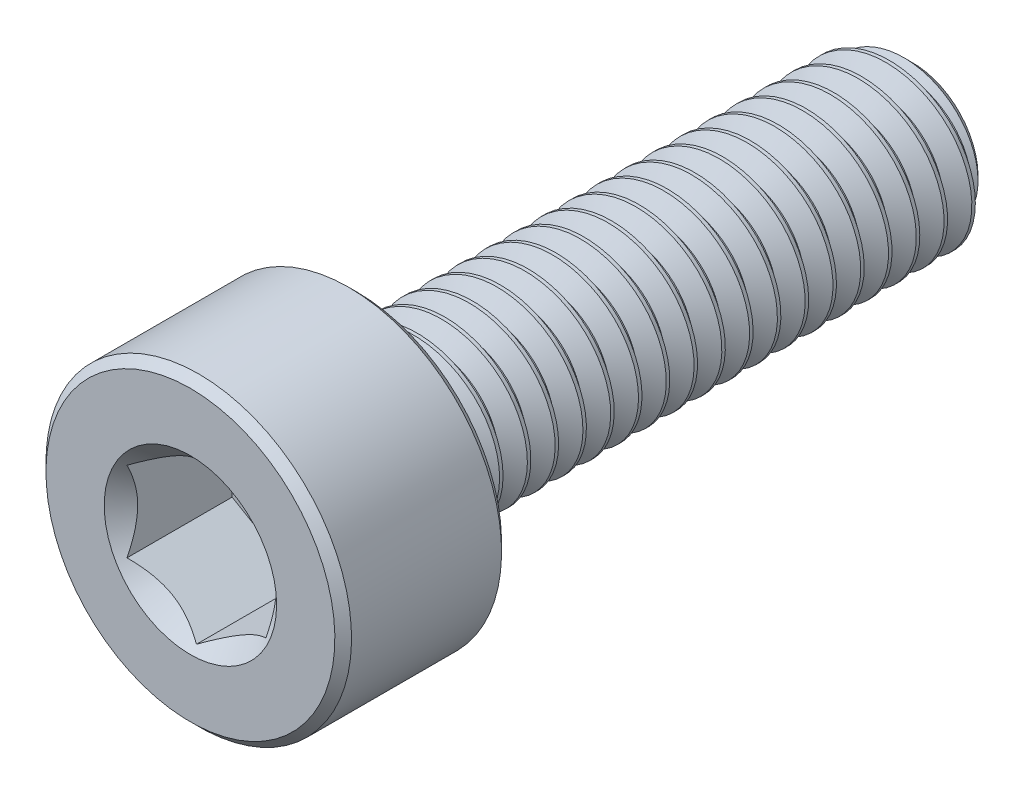
SolidWorks part; units mm, degrees
ref_plane "Front Plane" through (0, 0, 0) normal (0, 0, 1) x (1, 0, 0)
ref_plane "Top Plane" through (0, 0, 0) normal (0, 1, 0) x (1, 0, 0)
ref_plane "Right Plane" through (0, 0, 0) normal (1, 0, 0) x (0, 0, -1)
sketch "Sketch1" plane through (0, 0, 0) normal (1, 0, 0) x (0, 0, -1)
  line L0 (-6.5, 0) -> (6.5, 0) construction
  line L1 (6.5, 0) -> (6.5, 1.1752) construction
  line L2 (6.5, 1.1752) -> (6.1752, 1.5) construction
  line L3 (6.1752, 1.5) -> (6.125, 1.5) construction
  line L4 (6.125, 1.5) -> (-3.5, 1.5) construction
  line L5 (-3.5, 1.5) -> (-3.5, 2.75) construction
  line L6 (-3.5, 2.75) -> (-6.5, 2.75) construction
  line L7 (-6.5, 2.75) -> (-6.5, 0) construction
  line L8 (6.5, 1.1752) -> (6.5, 1.5) construction
  line L9 (6.4688, 1.5541) -> (6.7188, 1.1211) construction
  line L10 (6.7188, 1.1211) -> (6.9687, 1.5541) construction
  line L11 (6.9687, 1.5541) -> (6.4688, 1.5541) construction
  line L12 (6.7188, 1.5541) -> (6.7188, 1.5) construction
  line L13 (6.7188, 1.1211) -> (6.7188, 1.1752) construction
  line L14 (6.6875, 1.1752) -> (6.75, 1.1752) construction
  line L15 (6.5, 1.5) -> (6.9375, 1.5) construction
  line L16 (6.4844, 1.5271) -> (6.9531, 1.5271) construction
  line L17 (6.5, 0) -> (6.5, -1.5) construction
  line L18 (-3.65, 2.75) -> (-3.5, 2.6) construction
  line L19 (-6.35, 2.75) -> (-6.5, 2.6) construction
  line L20 (-3.5, 1.5) -> (-3.5, 0) construction
  line L21 (-3.5, 0.75) -> (-0.1667, 0.75) construction
  line L22 (-0.1667, 0.75) -> (3.1667, 0.75) construction
  line L23 (3.1667, 0.75) -> (6.5, 0.75) construction
  line L24 (-0.1667, 0.75) -> (-0.1667, 1.5) construction
  line L25 (-0.1667, 1.5) -> (-0.1667, 2.75) construction
  line L26 (3.1667, 0.75) -> (3.1667, 2.75) construction
  point P0 (-6.5, 1.25)
  point P3 (5.25, 1.5)
  point P4 (0, 0)
  point P18 (3.1667, 1.5)
  point P22 (6.7188, 1.1752)
  point P24 (6.125, 1.5)
  point P25 (6.7188, 1.5)
  point P28 (6.7187, 1.5271)
  point P29 (5.25, -1.5)
  point P30 (-0.1667, 1.5)
  point P31 (-5, 2.75)
  point P37 (-4.025, 2.75)
  point P38 (-6.275, 2.75)
  point P45 (-0.1667, 0.75)
  point P46 (3.1667, 0.75)
  dimension "D2" = 0.0625
  dimension "D7" = 0.15
  dimension "D8" = 0.15
  dimension "D9" = 0.15
  dimension "D10" = 0.075
  dimension "D11" = 0.375
  dimension "Drive Size" = 2.5
  dimension "Head Diameter" = 5.5
  dimension "Head Height" = 3
  dimension "Thread Pitch" = 0.5
  dimension "Thread Dia" = 3
  dimension "Length" = 10
  dimension "D12" = 0.375
  dimension "D4" = 1.25
  dimension "D3" = 45
sketch "Sketch2" plane through (0, 0, 0) normal (1, 0, 0) x (0, 0, -1)
  line L0 (-6.5, 0) -> (-6.5, 2.6)
  line L1 (-6.35, 2.75) -> (-3.65, 2.75)
  line L2 (-3.5, 2.6) -> (-3.5, 1.65)
  line L4 (6.1752, 1.5) -> (6.5, 1.1752)
  line L5 (6.5, 1.1752) -> (6.5, 0)
  line L6 (-3.5, 2.75) -> (-6.5, 2.75) construction
  line L7 (6.5, 0) -> (-6.5, 0)
  line L8 (-6.35, 2.75) -> (-6.5, 2.6) construction
  line L10 (-6.35, 2.75) -> (-6.5, 2.6)
  line L14 (-3.65, 2.75) -> (-3.5, 2.6) construction
  line L16 (-3.65, 2.75) -> (-3.5, 2.6)
  line L17 (-3.5, 1.5) -> (-3.5, 2.75) construction
  line L19 (-3.35, 1.5) -> (6.1752, 1.5)
  line L20 (6.125, 1.5) -> (-3.5, 1.5) construction
  arc A1 (-3.5, 1.65) -> (-3.35, 1.5) centre (-3.35, 1.65) ccw
  dimension "D3" = 0.15
revolve "Revolve1" add sketch "Sketch2" angle 360 about L7
sketch "Sketch3" plane through (0, 0, 6.5) normal (0, 0, 1) x (1, 0, 0)
  line L1 (1.25, -0.7217) -> (1.25, 0.7217)
  line L2 (1.25, 0.7217) -> (0, 1.4434)
  line L3 (0, 1.4434) -> (-1.25, 0.7217)
  line L4 (-1.25, 0.7217) -> (-1.25, -0.7217)
  line L5 (-1.25, -0.7217) -> (0, -1.4434)
  line L6 (0, -1.4434) -> (1.25, -0.7217)
  circle A0 centre (0, 0) radius 1.25 construction
  circle A1 centre (0, 0) radius 2.75 construction
  circle A2 centre (0, 0) radius 2.75 construction
  circle A3 centre (0, 0) radius 1.4434 construction
  point P13 (0, 0)
  dimension "D1" = 2.8868
extrude "Cut-Extrude1" cut sketch "Sketch3" against normal offset from surface (2 mm away) 1 up to face at (0, 2.6, 3.5)
sketch "Sketch4" plane through (0, 0, 6.5) normal (0, 0, 1) x (1, 0, 0)
  circle A0 centre (0, 0) radius 1.5516
  dimension "D1" = 3.1033
extrude "Cut-Extrude2" cut sketch "Sketch4" against normal up to vertex (1.5 mm away) draft 45 up to point (0, 2.75, 5)
sketch "Sketch11" plane through (0, 0, 0) normal (1, 0, 0) x (0, 0, -1)
  line L0 (-6.5, 0) -> (6.5, 0) construction
  line L1 (-6.5, 0) -> (6.5, 0) construction
  line L2 (-1.625, 0) -> (-1.625, 1.5) construction
  line L3 (6.125, 1.5) -> (-3.5, 1.5) construction
  line L4 (4.625, 0) -> (4.625, 1.5) construction
  line L6 (6.5, 1.1752) -> (6.5, 1.5) construction
  point P2 (-1.625, 0)
  point P3 (4.625, 0)
  dimension "D1" = 1.875
  dimension "D2" = 1.875
sketch "Sketch6" plane through (0, 0, -6.5) normal (0, 0, -1) x (-1, 0, 0)
  circle A0 centre (0, 0) radius 1.5
curve "Helix/Spiral1" pitch 0.5 height 10.5 turns 21
sketch "Sketch10" plane through (0, 0, 0) normal (1, 0, 0) x (0, 0, -1)
  line L0 (-3.35, -2.75) -> (-3.35, 2.75)
  line L5 (-6.5, 0) -> (6.5, 0) construction
  line L6 (-3.35, 1.5) -> (-3.35, -1.5) construction
  point P3 (-3.35, 0)
split "Split1" trim tools "Sketch10" bodies to split 106 resulting bodies 114 115
sketch "Sketch7" plane through (0, 0, 0) normal (1, 0, 0) x (0, 0, -1)
  line L0 (6.4844, 1.5271) -> (6.9531, 1.5271)
  line L1 (6.9531, 1.5271) -> (6.75, 1.1752)
  line L2 (6.75, 1.1752) -> (6.6875, 1.1752)
  line L3 (6.6875, 1.1752) -> (6.4844, 1.5271)
sweep "Cut-Sweep1" cut profiles "Sketch7" path "Helix/Spiral1"
sketch "Sketch8" plane through (0, 0, 0) normal (1, 0, 0) x (0, 0, -1)
  line L0 (-3.5, 0) -> (-3.5, 1.5)
  line L1 (-3.35, -1.5) -> (-3.35, 1.5) construction
  line L2 (-3.5, 1.5) -> (-3.35, 1.5)
  line L4 (-3.35, 1.5) -> (-2.484, 0)
  line L5 (-2.484, 0) -> (-3.5, 0)
  line L6 (6.125, 1.5) -> (-3.5, 1.5) construction
  line L7 (-6.5, 0) -> (6.5, 0) construction
  dimension "D1" = 60
revolve "Revolve2" add sketch "Sketch8" angle 360 about L5
equation "\"D2@Sketch1\" = \"Thread Pitch@Sketch1\" / 8"
equation "\"D4@Helix/Spiral1\" = \"Thread Pitch@Sketch1\""
equation "\"D7@Sketch1\" = \"Head Height@Sketch1\" * .05"
equation "\"D8@Sketch1\"=\"D7@Sketch1\""
equation "\"D9@Sketch1\"=\"D7@Sketch1\""
equation "\"D10@Sketch1\"=\"D7@Sketch1\"/2"
equation "\"D11@Sketch1\"=\"D10@Sketch1\"*5"
equation "\"D4@Sketch1\"=\"Thread Pitch@Sketch1\"*2.5"
equation "\"D12@Sketch1\"=\"Thread Pitch@Sketch1\"*.75"
equation "\"D3@Helix/Spiral1\"=\"Length@Sketch1\"+\"Thread Pitch@Sketch1\""
equation "\"D3@Sketch2\"=\"Thread Dia@Sketch1\"*0.05"
equation "\"D1@Sketch11\"=\"Length@Sketch1\"*0.1875"
equation "\"D2@Sketch11\"=\"D1@Sketch11\""
equation "\"D1@Sketch4\"=\"D1@Sketch3\"*1.075"
